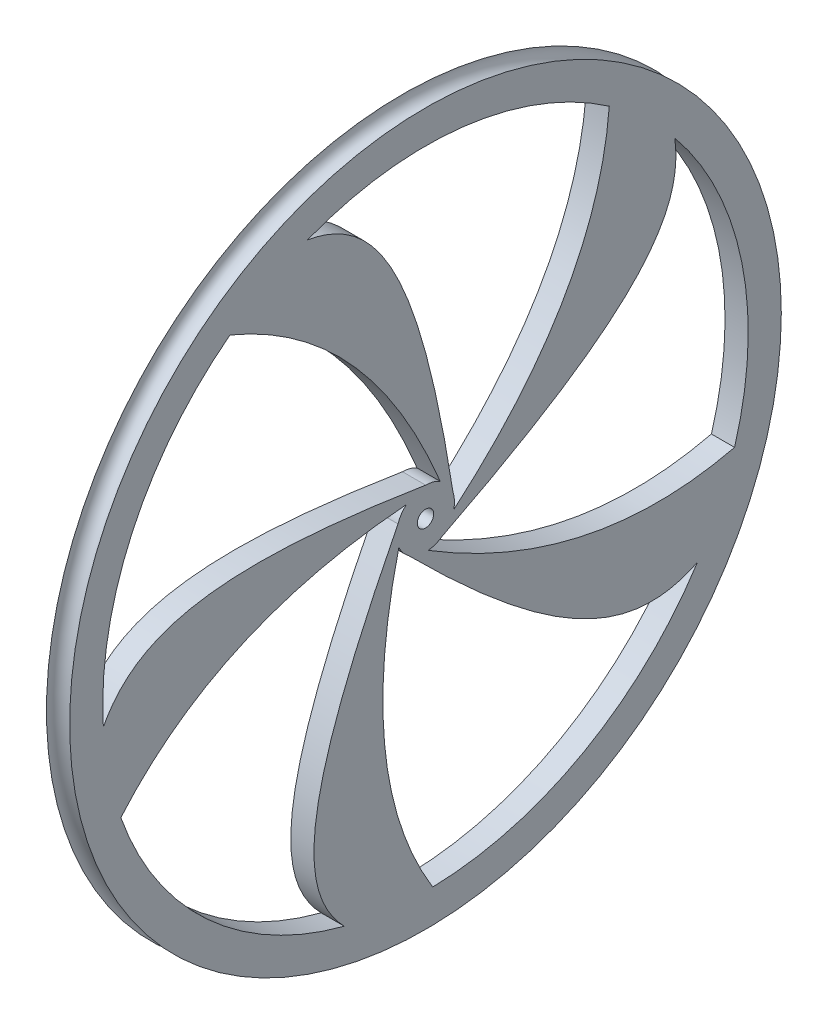
SolidWorks part; units mm, degrees
ref_plane "Front Plane" through (0, 0, 0) normal (0, 0, 1) x (1, 0, 0)
ref_plane "Top Plane" through (0, 0, 0) normal (0, 1, 0) x (1, 0, 0)
ref_plane "Right Plane" through (0, 0, 0) normal (1, 0, 0) x (0, 0, -1)
sketch "Sketch1" plane through (0, 0, 0) normal (0, 0, 1) x (1, 0, 0)
  line L0 (0, 0) -> (-8.3638, 0) construction
  line L1 (-1.778, 49.53) -> (1.778, 49.53)
  line L2 (-1.778, 49.53) -> (-1.778, 54.61)
  line L4 (1.778, 49.53) -> (1.778, 54.61)
  arc A0 (-1.778, 54.61) -> (1.778, 54.61) centre (0, 54.61) ccw
  point P7 (0, 49.53)
  dimension "D1" = 1.778
  dimension "D2" = 5.08
  dimension "D3" = 54.61
  dimension "D4" = 8.3638
revolve "Revolve1" add sketch "Sketch1" angle 360 about L0
sketch "Sketch3" plane through (0, 0, 0) normal (1, 0, 0) x (0, 0, -1)
  line L0 (1.0889, 0.6286) -> (-1.0889, 0.6286)
  circle A0 centre (0, 0) radius 1.2573
  circle A1 centre (0, 0) radius 4.445
  dimension "D1" = 2.5146
  dimension "D2" = 8.89
extrude "Boss-Extrude1" add sketch "Sketch3" along normal mid plane 3.556 separate body contours A1 A0
sketch "Sketch4" plane through (0, 0, 0) normal (1, 0, 0) x (0, 0, -1)
  line L0 (-4.445, 0) -> (4.445, 0) construction
  line L1 (-172.1158, 39.362) -> (67.2282, 47.9926) construction
  line L2 (-21.8469, 172.0075) -> (30.7369, -172.0075) construction
  circle A0 centre (0, 0) radius 49.53 construction
  circle A1 centre (0, 0) radius 49.53
  circle A2 centre (0, 0) radius 4.445 construction
  circle A3 centre (0, 0) radius 4.445
  circle A4 centre (0, 0) radius 68.2499 construction
  spline S0 degree 3 poles (4.445, 0) (-0.663, 33.4177) (-11.9659, 51.9236) (-35.803, 44.2774) (-52.4438, 43.6773) knots 0 0 0 0 0.582841 1 1 1 1
  spline S1 degree 2 poles (2.269, 3.8222) (-14.0803, 43.377) (-52.4438, 43.6773) knots 0 0 0 1 1 1
  dimension "D1" = 72.3398
  dimension "D2" = 136.4999
  dimension "D5" = 2.065
  dimension "D6" = 81.309
  dimension "D7" = 101.4175
  dimension "D8" = 49.9547
  dimension "D9" = 88.9045
  dimension "D3" = 3.8222
  dimension "D4" = 43.6773
extrude "Boss-Extrude2" add sketch "Sketch4" along normal mid plane 3.556 contours S1 A3 S0 A1
pattern_circular "CirPattern1" count 5 over 360 of "Boss-Extrude2"
